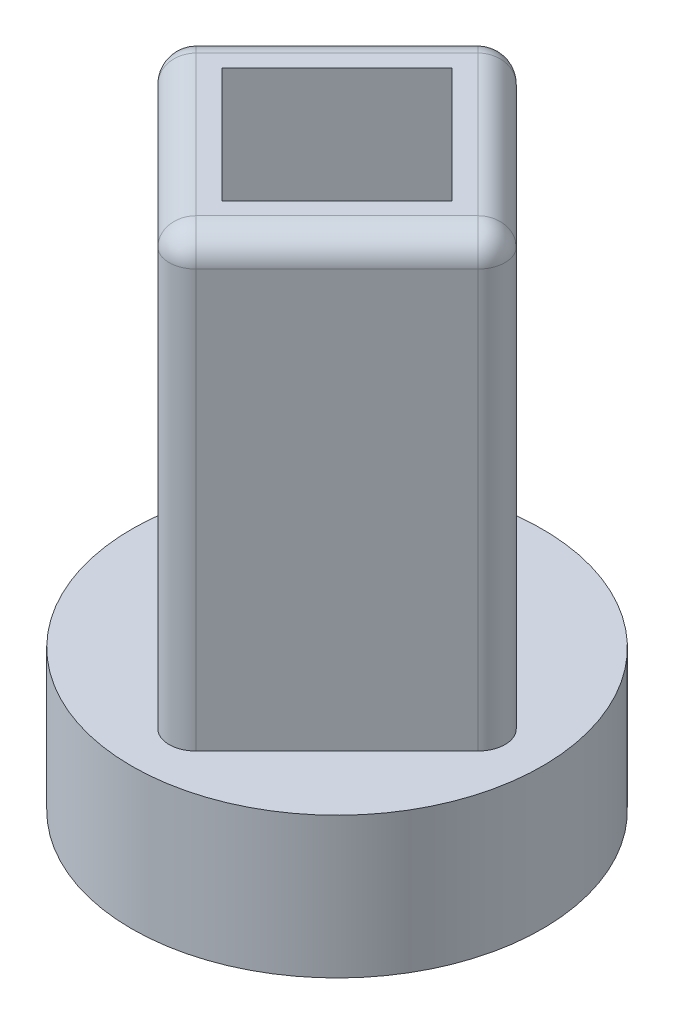
SolidWorks part; units mm, degrees
ref_plane "Front Plane" through (0, 0, 0) normal (0, 0, 1) x (1, 0, 0)
ref_plane "Top Plane" through (0, 0, 0) normal (0, 1, 0) x (1, 0, 0)
ref_plane "Right Plane" through (0, 0, 0) normal (1, 0, 0) x (0, 0, -1)
sketch "Sketch1" plane through (0, 0, 0) normal (0, 1, 0) x (1, 0, 0)
  circle A0 centre (0, 0) radius 7.575
  dimension "D1" = 15.15
extrude "Boss-Extrude1" add sketch "Sketch1" along normal blind 5.2
sketch "Sketch2" plane through (0, 0, 0) normal (0, -1, 0) x (1, 0, 0)
  line L0 (-4.3593, -1.3881) -> (0, -4.575)
  arc A0 (0, -4.575) -> (-4.3593, -1.3881) centre (0, 0) ccw
  dimension "D1" = 9.15
  dimension "D2" = 5.4
extrude "Cut-Extrude1" cut sketch "Sketch2" against normal blind 3.6
sketch "Sketch3" plane through (0, 3.6, 0) normal (0, -1, 0) x (1, 0, 0)
  line L0 (-1.9, 2.1577) -> (1.9, 2.1577)
  arc A0 (-1.9, 2.1577) -> (1.9, 2.1577) centre (0, 0) ccw
  dimension "D1" = 5.75
  dimension "D2" = 3.8
sketch "Sketch4" plane through (0, 5.2, 0) normal (0, 1, 0) x (1, 0, 0)
  line L1 (4.2426, 0) -> (0, 4.2426)
  line L2 (0, 4.2426) -> (-4.2426, 0)
  line L3 (-4.2426, 0) -> (0, -4.2426)
  line L4 (0, -4.2426) -> (4.2426, 0)
  line L5 (6.6114, 0) -> (0, 6.6114)
  line L6 (0, 6.6114) -> (-6.6114, 0)
  line L7 (-6.6114, 0) -> (0, -6.6114)
  line L8 (0, -6.6114) -> (6.6114, 0)
  circle A0 centre (0, 0) radius 3 construction
  circle A1 centre (0, 0) radius 4.675 construction
  dimension "D1" = 6
  dimension "D2" = 9.35
extrude "Boss-Extrude2" add sketch "Sketch4" along normal blind 16.4
fillet "Fillet1" radius 1 8 edges at (-3.3057, 21.6, -3.3057) (-3.3057, 21.6, 3.3057) (3.3057, 21.6, 3.3057) (3.3057, 21.6, -3.3057) (6.6114, 13.4, 0) (0, 13.4, 6.6114) (-6.6114, 13.4, 0) (0, 13.4, -6.6114)
sketch "Sketch5" plane through (0, 5.2, 0) normal (0, 1, 0) x (1, 0, 0)
  line L4 (0, -4.2426) -> (4.2426, 0)
  line L5 (4.2426, 0) -> (0, 4.2426)
  line L6 (0, 4.2426) -> (-4.2426, 0)
  line L7 (-4.2426, 0) -> (0, -4.2426)
  line L8 (0, -4.2426) -> (4.2426, 0)
  line L9 (4.2426, 0) -> (0, 4.2426)
  line L10 (0, 4.2426) -> (-4.2426, 0)
  line L11 (-4.2426, 0) -> (0, -4.2426)
  dimension "D1" = 0
extrude "Boss-Extrude3" add sketch "Sketch5" along normal blind 4.85
sketch "Sketch6" plane through (0, 10.05, 0) normal (0, 1, 0) x (1, 0, 0)
  circle A0 centre (0, 0) radius 1.875
  dimension "D1" = 3.75
extrude "Boss-Extrude4" add sketch "Sketch6" along normal blind 2.55
extrude "Cut-Extrude2" cut sketch "Sketch3" against normal blind 4
